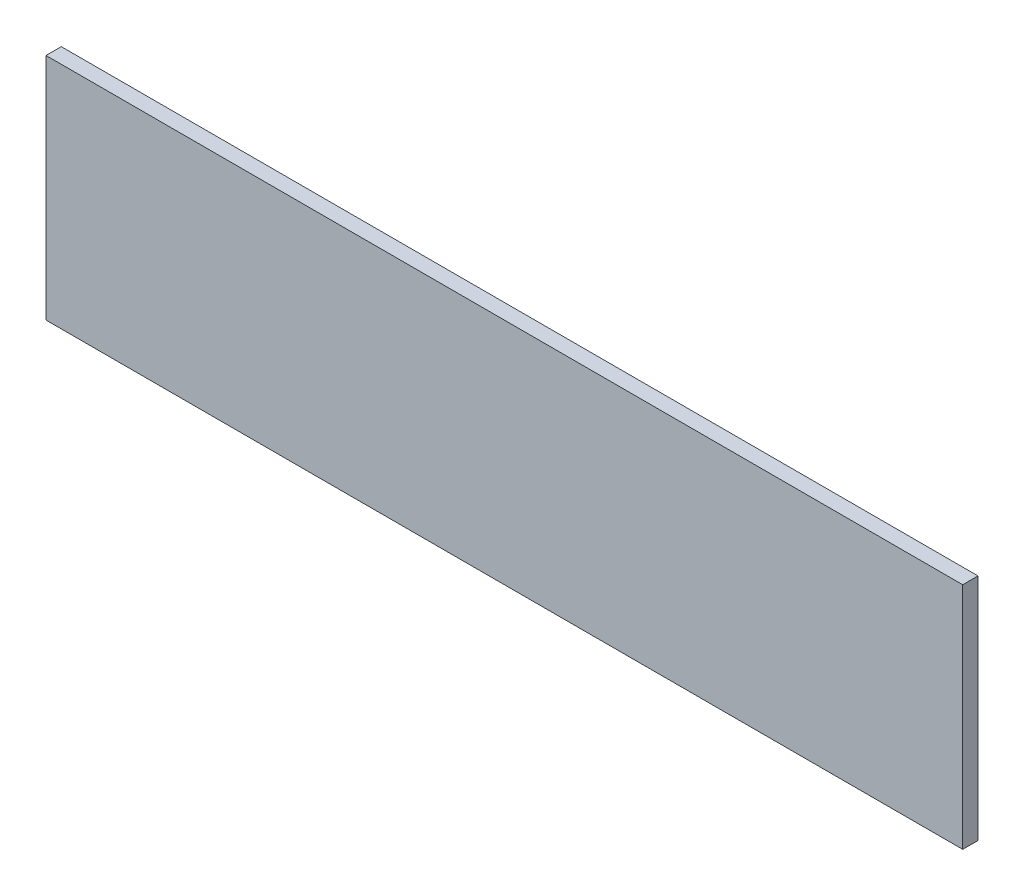
SolidWorks part; units mm, degrees
ref_plane "正面" through (0, 0, 0) normal (0, 0, 1) x (1, 0, 0)
ref_plane "平面" through (0, 0, 0) normal (0, 1, 0) x (1, 0, 0)
ref_plane "右側面" through (0, 0, 0) normal (1, 0, 0) x (0, 0, -1)
sketch "ｽｹｯﾁ1" plane through (0, 0, 0) normal (0, 0, 1) x (1, 0, 0)
  line L1 (0, 0) -> (24, 0)
  line L2 (0, 0) -> (0, 6)
  line L3 (0, 6) -> (24, 6)
  line L4 (24, 0) -> (24, 6)
  dimension "D1" = 24
  dimension "D2" = 6
extrude "ﾎﾞｽ - 押し出し1" add sketch "ｽｹｯﾁ1" along normal blind 0.4
